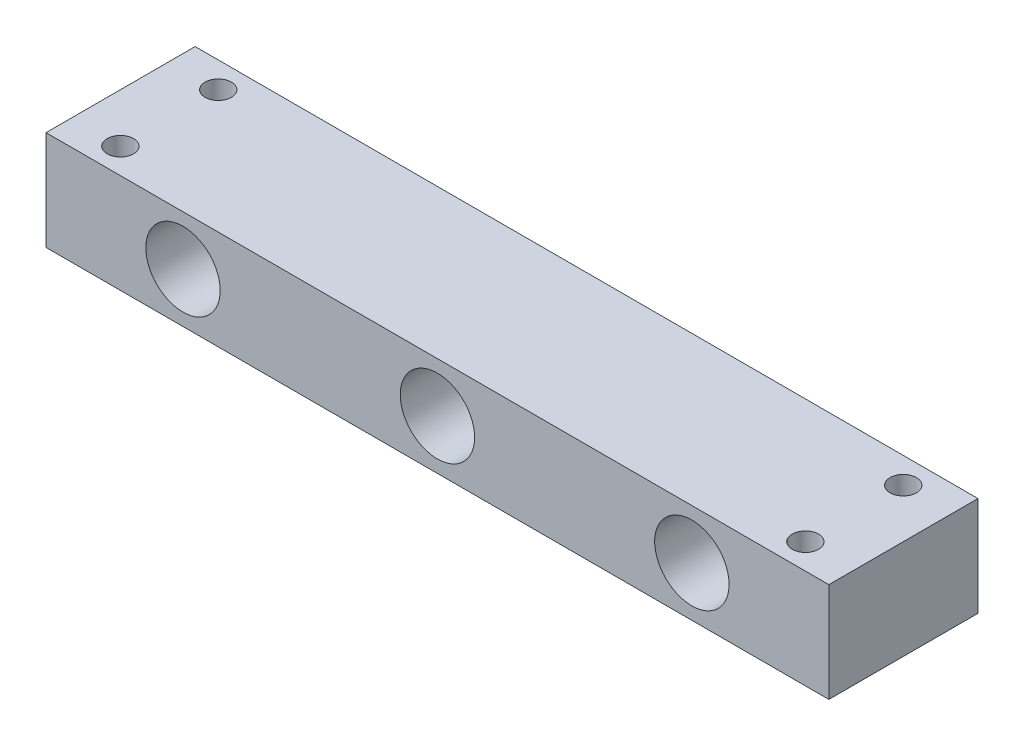
SolidWorks part; units mm, degrees
ref_plane "Front Plane" through (0, 0, 0) normal (0, 0, 1) x (1, 0, 0)
ref_plane "Top Plane" through (0, 0, 0) normal (0, 1, 0) x (1, 0, 0)
ref_plane "Right Plane" through (0, 0, 0) normal (1, 0, 0) x (0, 0, -1)
sketch "Sketch1" plane through (0, 0, 0) normal (0, 1, 0) x (1, 0, 0)
  line L1 (0, 0) -> (400, 0)
  line L2 (0, 0) -> (0, 76.2)
  line L3 (0, 76.2) -> (400, 76.2)
  line L4 (400, 0) -> (400, 76.2)
  dimension "D1" = 76.2
  dimension "D2" = 400
extrude "Boss-Extrude1" add sketch "Sketch1" along normal blind 50.8
sketch "Sketch3" plane through (0, 50.8, 0) normal (0, 1, 0) x (1, 0, 0)
  line L1 (0, 0) -> (200, 0)
  line L2 (0, 0) -> (0, 38)
  line L3 (0, 38) -> (200, 38)
  line L4 (200, 0) -> (200, 38)
  line L5 (25, 63) -> (375, 63)
  line L6 (25, 63) -> (25, 13)
  line L7 (25, 13) -> (375, 13)
  line L8 (375, 63) -> (375, 13)
  line L9 (25, 63) -> (375, 13) construction
  line L10 (25, 13) -> (375, 63) construction
  circle A0 centre (25, 63) radius 6.75
  circle A1 centre (25, 13) radius 6.75
  circle A2 centre (375, 63) radius 6.75
  circle A3 centre (375, 13) radius 6.75
  dimension "D1" = 200
  dimension "D2" = 38
  dimension "D3" = 350
  dimension "D4" = 50
extrude "Cut-Extrude2" cut sketch "Sketch3" against normal blind 50.8 contours A2 | A1 | A3 | A0
sketch "Sketch5" plane through (0, 0, 0) normal (0, 0, 1) x (1, 0, 0)
  line L0 (200, 25.4) -> (330, 25.4)
  line L1 (0, 0) -> (200, 0)
  line L2 (0, 0) -> (0, 25.4)
  line L4 (200, 0) -> (200, 25.4)
  line L5 (200, 25.4) -> (70, 25.4)
  circle A0 centre (200, 25.4) radius 19
  circle A1 centre (70, 25.4) radius 19
  circle A2 centre (330, 25.4) radius 19
  dimension "D3" = 130
  dimension "D1" = 25.4
  dimension "D2" = 200
  dimension "D4" = 130
extrude "Cut-Extrude3" cut sketch "Sketch5" against normal through all
